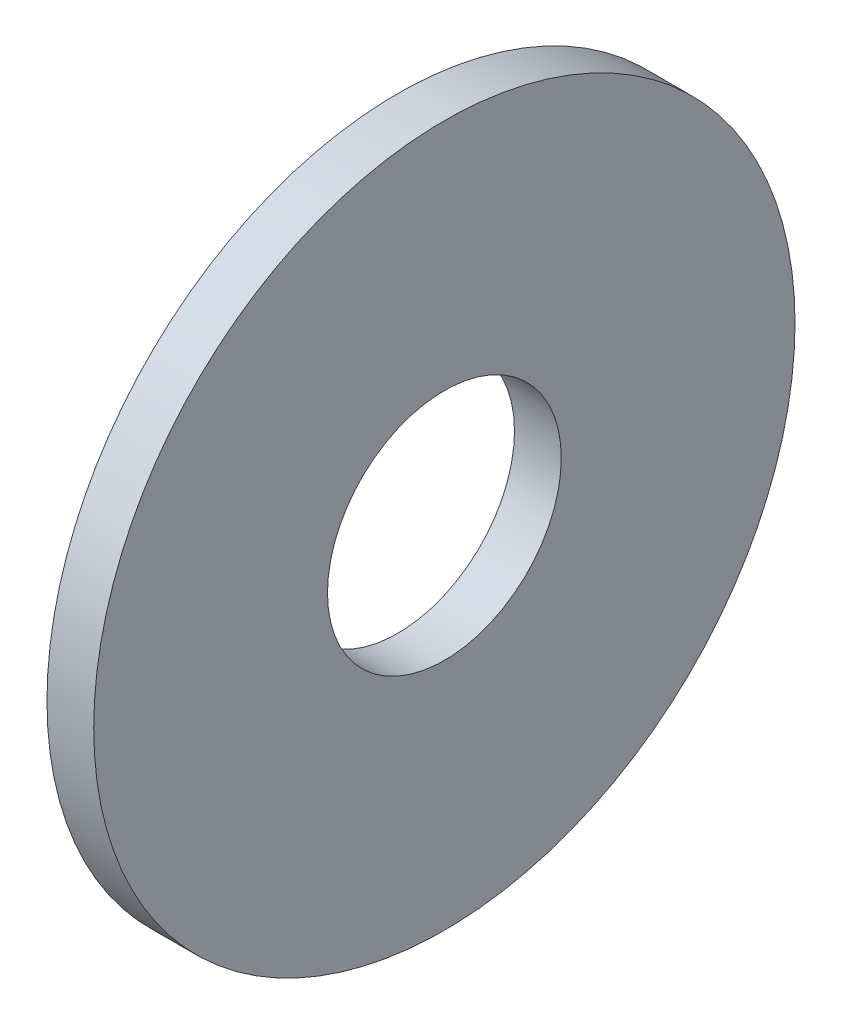
SolidWorks part; units mm, degrees
ref_plane "Front Plane" through (0, 0, 0) normal (0, 0, 1) x (1, 0, 0)
ref_plane "Top Plane" through (0, 0, 0) normal (0, 1, 0) x (1, 0, 0)
ref_plane "Right Plane" through (0, 0, 0) normal (1, 0, 0) x (0, 0, -1)
sketch "Sketch1" plane through (0, 0, 0) normal (1, 0, 0) x (0, 0, -1)
  circle A0 centre (0, 0) radius 7.5
  circle A1 centre (0, 0) radius 2.5
  dimension "D1" = 5
  dimension "D2" = 15
extrude "Boss-Extrude1" add sketch "Sketch1" along normal blind 1
